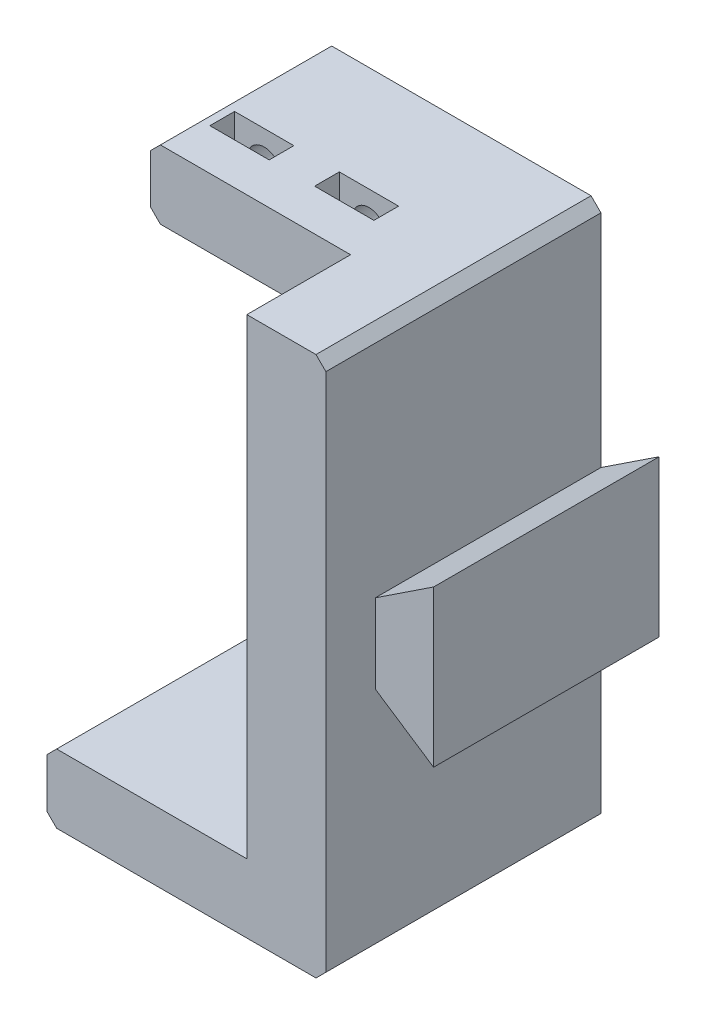
SolidWorks part; units mm, degrees
ref_plane "Front Plane" through (0, 0, 0) normal (0, 0, 1) x (1, 0, 0)
ref_plane "Top Plane" through (0, 0, 0) normal (0, 1, 0) x (1, 0, 0)
ref_plane "Right Plane" through (0, 0, 0) normal (1, 0, 0) x (0, 0, -1)
sketch "Sketch5" plane through (0, 0, 0) normal (0, 0, 1) x (1, 0, 0)
  line L0 (0, 20.375) -> (0, 0)
  line L1 (0, 0) -> (8, 0)
  line L2 (8, 0) -> (8, 27.325)
  line L3 (8, 27.325) -> (-20.25, 27.325)
  line L4 (-20.25, 27.325) -> (-20.25, 20.375)
  line L5 (-20.25, 20.375) -> (0, 20.375)
  line L6 (8, 4) -> (13.9, 7.9)
  line L7 (13.9, 7.9) -> (13.9, 0)
  line L8 (13.9, 0) -> (8, 0)
  line L9 (13.9, 0) -> (8, 0)
  line L10 (8, 4) -> (8, 0)
  line L11 (27.875, 0) -> (-34.5649, 0) construction
  dimension "D1" = 7.9
  dimension "D2" = 4
  dimension "D3" = 5.9
  dimension "D4" = 8
  dimension "D5" = 20.25
  dimension "D6" = 40.75
  dimension "D7" = 6.95
extrude "Boss-Extrude1" add sketch "Sketch5" along normal blind 27.84 contours L8 L7 L6 L2 | L4 L5 L0 L1 L2 L3
sketch "Sketch6" plane through (0, 0, 0) normal (0, 0, -1) x (-1, 0, 0)
  line L1 (-8, 27.325) -> (20.25, 27.325) construction
  line L2 (0, 20.375) -> (0, 0) construction
  circle A0 centre (4.83, 24.005) radius 1.7
  circle A1 centre (15.43, 24.005) radius 1.7
  dimension "D4" = 3.4
  dimension "D1" = 3.32
  dimension "D2" = 4.83
  dimension "D3" = 10.6
extrude "Cut-Extrude1" cut sketch "Sketch6" against normal blind 13.15
sketch "Sketch7" plane through (0, 27.325, 0) normal (0, 1, 0) x (1, 0, 0)
  line L0 (-3.13, -13.15) -> (-6.53, -13.15) construction
  line L1 (-1.83, -10.65) -> (-7.83, -10.65)
  line L2 (-1.83, -10.65) -> (-1.83, -13.15)
  line L3 (-1.83, -13.15) -> (-7.83, -13.15)
  line L4 (-7.83, -10.65) -> (-7.83, -13.15)
  line L5 (-12.43, -10.65) -> (-18.43, -10.65)
  line L6 (-12.43, -10.65) -> (-12.43, -13.15)
  line L7 (-12.43, -13.15) -> (-18.43, -13.15)
  line L8 (-18.43, -10.65) -> (-18.43, -13.15)
  line L9 (-4.83, 0) -> (-4.83, -27.84) construction
  line L10 (-15.43, 0) -> (-15.43, -27.84) construction
  line L11 (8, -27.84) -> (-20.25, -27.84) construction
  point P8 (-4.83, -10.65)
  point P13 (-15.43, -10.65)
  dimension "D1" = 6
  dimension "D2" = 2.5
extrude "Cut-Extrude2" cut sketch "Sketch7" against normal blind 6
chamfer "Chamfer1" distance 1 angle 45 3 edges at (-20.25, 20.375, 13.92) (8, 27.325, 13.92) (-20.25, 27.325, 13.92)
mirror "Mirror2" about plane through (0, 0, 27.84) normal (0, -1, 0) of "Cut-Extrude2", "Cut-Extrude1", "Boss-Extrude1", "Chamfer1"
sketch "Sketch8" plane through (8, 0, 0) normal (1, 0, 0) x (0, 0, -1)
  line L0 (-27.84, 4) -> (-27.84, 26.325) construction
  line L1 (-27.84, 7.9) -> (-22.84, 7.9)
  line L2 (-27.84, 7.9) -> (-27.84, -7.9)
  line L3 (-27.84, -7.9) -> (-22.84, -7.9)
  line L4 (-22.84, 7.9) -> (-22.84, -7.9)
  dimension "D1" = 5
extrude "Cut-Extrude3" cut sketch "Sketch8" along normal through all
sketch "Sketch9" plane through (0, 27.325, 0) normal (0, 1, 0) x (1, 0, 0)
  line L0 (7, -27.84) -> (-19.25, -27.84) construction
  line L1 (-13.5, -17.34) -> (-6.5, -17.34) construction
  line L2 (-13.5, -17.34) -> (-13.5, -21.34) construction
  line L3 (-13.5, -21.34) -> (-6.5, -21.34) construction
  line L4 (-6.5, -17.34) -> (-6.5, -21.34) construction
  line L5 (-13.5, -17.34) -> (-6.5, -21.34) construction
  line L6 (-13.5, -21.34) -> (-6.5, -17.34) construction
  line L9 (0, -17.34) -> (-20.25, -17.34)
  line L10 (0, -17.34) -> (0, -27.84)
  line L11 (0, -27.84) -> (-20.25, -27.84)
  line L12 (-20.25, -17.34) -> (-20.25, -27.84)
  point P0 (-10, -19.34)
  dimension "D1" = 6.5
  dimension "D2" = 4
  dimension "D3" = 7
  dimension "D4" = 10
extrude "Cut-Extrude4" cut sketch "Sketch9" against normal up to next
